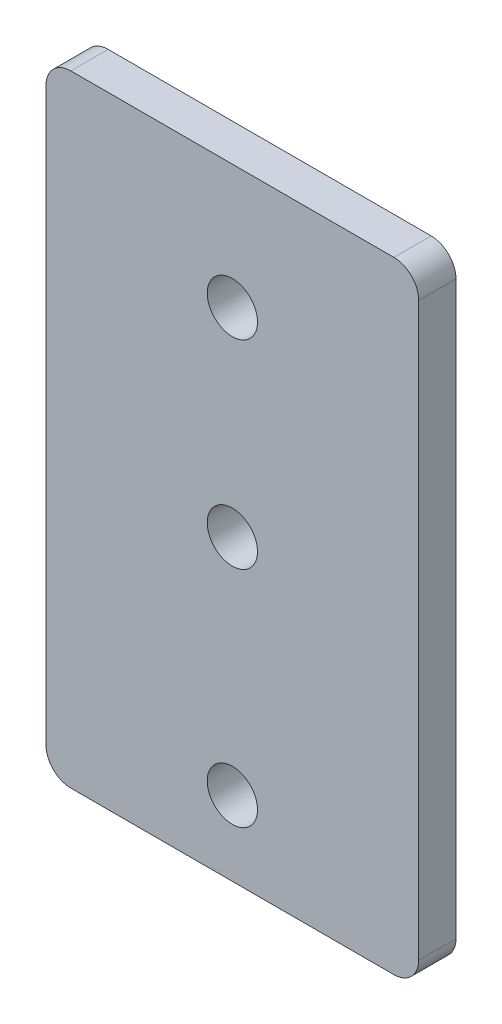
SolidWorks part; units mm, degrees
material "环氧玻璃布层压板"
ref_plane "前视基准面" through (0, 0, 0) normal (0, 0, 1) x (1, 0, 0)
ref_plane "上视基准面" through (0, 0, 0) normal (0, 1, 0) x (1, 0, 0)
ref_plane "右视基准面" through (0, 0, 0) normal (1, 0, 0) x (0, 0, -1)
sketch "草图1" plane through (0, 0, 0) normal (0, 0, 1) x (1, 0, 0)
  line L1 (-15, -25) -> (15, -25)
  line L2 (-15, -25) -> (-15, 25)
  line L3 (-15, 25) -> (15, 25)
  line L4 (15, -25) -> (15, 25)
  line L5 (0, 25) -> (0, -25) construction
  line L6 (-15, 0) -> (15, 0) construction
  point P0 (0, 0)
  dimension "D1" = 30
  dimension "D2" = 50
extrude "凸台-拉伸1" add sketch "草图1" along normal blind 3
sketch "草图2" plane through (0, 0, 3) normal (0, 0, 1) x (1, 0, 0)
  line L0 (-15, 5) -> (15, 5) construction
  line L1 (-15, 25) -> (-15, -25) construction
  line L2 (15, -25) -> (15, 25) construction
  line L3 (15, 25) -> (-15, 25) construction
  line L4 (0, 25) -> (0, 5) construction
  circle A0 centre (0, 15) radius 2.025
  dimension "D2" = 4.05
  dimension "D1" = 20
extrude "切除-拉伸1" cut sketch "草图2" against normal blind 4
sketch "草图3" plane through (0, 0, 3) normal (0, 0, 1) x (1, 0, 0)
  line L0 (-15, 5) -> (15, 5) construction
  line L1 (-15, 25) -> (-15, -25) construction
  line L2 (15, -25) -> (15, 25) construction
  line L3 (15, 25) -> (-15, 25) construction
  line L4 (0, 5) -> (0, -25) construction
  line L5 (-15, -25) -> (15, -25) construction
  circle A0 centre (0, -1) radius 2.025
  circle A1 centre (0, -19) radius 2.025
  circle A2 centre (0, 15) radius 2.025 construction
  dimension "D1" = 20
  dimension "D2" = 6
  dimension "D3" = 6
extrude "切除-拉伸2" cut sketch "草图3" against normal blind 34
fillet "圆角1" radius 2 4 edges at (-15, 25, 1.5) (15, 25, 1.5) (15, -25, 1.5) (-15, -25, 1.5)
equation "\"D3@草图3\"=\"D2@草图3\""
